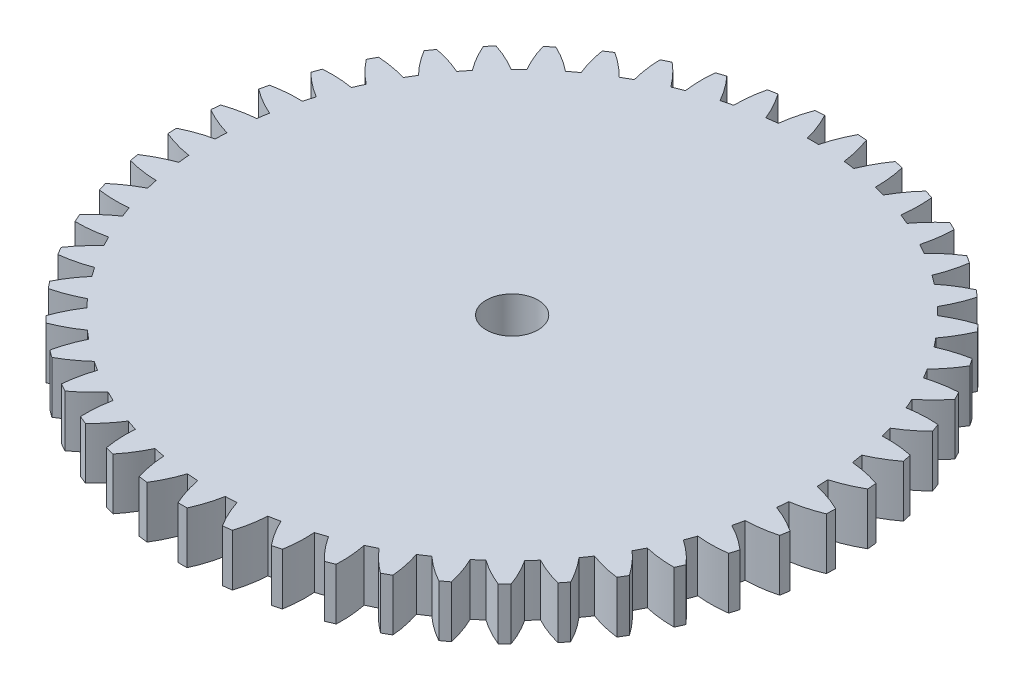
SolidWorks part; units mm, degrees
ref_plane "Front Plane" through (0, 0, 0) normal (0, 0, 1) x (1, 0, 0)
ref_plane "Top Plane" through (0, 0, 0) normal (0, 1, 0) x (1, 0, 0)
ref_plane "Right Plane" through (0, 0, 0) normal (1, 0, 0) x (0, 0, -1)
sketch "Sketch1" plane through (0, 0, 0) normal (0, 1, 0) x (1, 0, 0)
  circle A0 centre (0, 0) radius 1.5875
  circle A1 centre (0, 0) radius 18.3 construction
  arc A2 (-2.018, 18.3293) -> (-2.6973, 18.2417) centre (0, 0) ccw
  arc A3 (-20.1966, -0.3688) -> (-20.1788, -0.9259) centre (0, 0) ccw
  arc A4 (2.018, 18.3293) -> (1.5722, 20.1387) centre (-5.7243, 17.3817) ccw
  arc A5 (-0.3425, 18.4368) -> (-1.016, 20.1744) centre (-7.9, 16.507) ccw
  arc A6 (1.016, 20.1744) -> (0.3425, 18.4368) centre (7.9, 16.507) ccw
  arc A7 (3.5875, 19.8789) -> (2.6973, 18.2417) centre (9.946, 15.3612) ccw
  arc A8 (4.3453, 17.9207) -> (4.1346, 19.7723) centre (-3.4546, 17.971) ccw
  arc A9 (6.1001, 19.2569) -> (5.0079, 17.747) centre (11.8287, 13.9632) ccw
  arc A10 (6.6013, 17.2179) -> (6.6291, 19.0813) centre (-1.1281, 18.2652) ccw
  arc A11 (8.5125, 18.3188) -> (7.2362, 16.9609) centre (13.5172, 12.336) ccw
  arc A12 (8.7488, 16.2324) -> (9.0147, 18.0769) centre (1.2168, 18.2595) ccw
  arc A13 (10.7852, 17.0798) -> (9.3457, 15.8963) centre (14.9837, 10.5062) ccw
  arc A14 (10.7528, 14.9804) -> (11.2523, 16.7757) centre (3.5418, 17.954) ccw
  arc A15 (12.8808, 15.5604) -> (11.3017, 14.5707) centre (16.2042, 8.5038) ccw
  arc A16 (12.5801, 13.4823) -> (13.3052, 15.1991) centre (5.8087, 17.3537) ccw
  arc A17 (14.7648, 13.7855) -> (13.0722, 13.0058) centre (17.1586, 6.3619) ccw
  arc A18 (14.2009, 11.7629) -> (15.1396, 13.3729) centre (7.9801, 16.4684) ccw
  arc A19 (16.4065, 11.7842) -> (14.628, 11.2274) centre (17.8312, 4.1155) ccw
  arc A20 (15.5886, 9.8504) -> (16.7253, 11.3271) centre (10.0205, 15.3127) ccw
  arc A21 (17.7787, 9.5895) -> (15.9437, 9.2646) centre (18.2111, 1.8015) ccw
  arc A22 (16.7202, 7.7761) -> (18.0365, 9.0953) centre (11.8964, 13.9056) ccw
  arc A23 (18.859, 7.2373) -> (16.9975, 7.1497) centre (18.292, -0.5421) ccw
  arc A24 (17.5773, 5.5741) -> (19.0515, 6.7142) centre (13.5769, 12.2702) ccw
  arc A25 (19.6297, 4.7662) -> (17.7722, 4.9174) centre (18.0725, -2.8768) ccw
  arc A26 (18.1458, 3.2806) -> (19.7537, 4.2228) centre (15.0345, 10.4332) ccw
  arc A27 (20.078, 2.2169) -> (18.2552, 2.6044) centre (17.5562, -5.1642) ccw
  arc A28 (18.4164, 0.9333) -> (20.1315, 1.6621) centre (16.2453, 8.425) ccw
  arc A29 (20.1966, -0.3688) -> (18.4383, 0.2486) centre (16.7517, -7.3669) ccw
  arc A30 (18.3845, -1.4294) -> (20.1788, -0.9259) centre (17.1893, 6.2784) ccw
  arc A31 (19.9837, -2.9485) -> (18.3187, -2.1113) centre (15.6721, -9.4485) ccw
  arc A32 (18.0508, -3.7687) -> (19.8947, -3.4987) centre (17.851, 4.0288) ccw
  arc A33 (19.4425, -5.4797) -> (17.8984, -4.4365) centre (14.3352, -11.3751) ccw
  arc A34 (17.4207, -6.046) -> (19.284, -6.0141) centre (18.2197, 1.713) ccw
  arc A35 (18.5822, -7.921) -> (17.1841, -6.6889) centre (12.7629, -13.1148) ccw
  arc A36 (16.5045, -8.2241) -> (18.3566, -8.4307) centre (18.2891, -0.631) ccw
  arc A37 (17.4167, -10.2322) -> (16.1877, -8.8314) centre (10.981, -14.6392) ccw
  arc A38 (15.3173, -10.2671) -> (17.1278, -10.7089) centre (18.0583, -2.9646) ccw
  arc A39 (15.9653, -12.3754) -> (14.9254, -10.8289) centre (9.0188, -15.9233) ccw
  arc A40 (13.8786, -12.1415) -> (15.6177, -12.8112) centre (17.5309, -5.2495) ccw
  arc A41 (14.2517, -14.3154) -> (13.4181, -12.6486) centre (6.9086, -16.9458) ccw
  arc A42 (12.2121, -13.8166) -> (13.8512, -14.7032) centre (16.7157, -7.4482) ccw
  arc A43 (12.304, -16.0203) -> (11.6905, -14.2607) centre (4.6849, -17.6902) ccw
  arc A44 (10.345, -15.2648) -> (11.8573, -16.3537) centre (15.626, -9.5246) ccw
  arc A45 (10.1544, -17.4622) -> (9.7709, -15.6385) centre (2.3842, -18.144) ccw
  arc A46 (8.308, -16.4624) -> (9.6687, -17.7357) centre (14.2798, -11.4446) ccw
  arc A47 (7.838, -18.6174) -> (7.6909, -16.7596) centre (0.0445, -18.2999) ccw
  arc A48 (6.1346, -17.3896) -> (7.3213, -18.8265) centre (12.699, -13.1767) ccw
  arc A49 (5.3929, -19.4668) -> (5.4845, -17.6055) centre (-2.2961, -18.1554) ccw
  arc A50 (3.8605, -18.0314) -> (4.8538, -19.6082) centre (10.9098, -14.6924) ccw
  arc A51 (2.8593, -19.9966) -> (3.1882, -18.1623) centre (-4.5989, -17.7127) ccw
  arc A52 (1.523, -18.377) -> (2.3065, -20.0679) centre (8.9414, -15.9669) ccw
  arc A53 (0.2787, -20.1981) -> (0.8395, -18.4209) centre (-6.8262, -16.9792) ccw
  arc A54 (-0.8395, -18.4209) -> (-0.2787, -20.1981) centre (6.8262, -16.9792) ccw
  arc A55 (-2.3065, -20.0679) -> (-1.523, -18.377) centre (-8.9414, -15.9669) ccw
  arc A56 (-3.1882, -18.1623) -> (-2.8593, -19.9966) centre (4.5989, -17.7127) ccw
  arc A57 (-4.8538, -19.6082) -> (-3.8605, -18.0314) centre (-10.9098, -14.6924) ccw
  arc A58 (-5.4845, -17.6055) -> (-5.3929, -19.4668) centre (2.2961, -18.1554) ccw
  arc A59 (-7.3213, -18.8265) -> (-6.1346, -17.3896) centre (-12.699, -13.1767) ccw
  arc A60 (-7.6909, -16.7596) -> (-7.838, -18.6174) centre (-0.0445, -18.2999) ccw
  arc A61 (-9.6687, -17.7357) -> (-8.308, -16.4624) centre (-14.2798, -11.4446) ccw
  arc A62 (-9.7709, -15.6385) -> (-10.1544, -17.4622) centre (-2.3842, -18.144) ccw
  arc A63 (-11.8573, -16.3537) -> (-10.345, -15.2648) centre (-15.626, -9.5246) ccw
  arc A64 (-11.6905, -14.2607) -> (-12.304, -16.0203) centre (-4.6849, -17.6902) ccw
  arc A65 (-13.8512, -14.7032) -> (-12.2121, -13.8166) centre (-16.7157, -7.4482) ccw
  arc A66 (-13.4181, -12.6486) -> (-14.2517, -14.3154) centre (-6.9086, -16.9458) ccw
  arc A67 (-15.6177, -12.8112) -> (-13.8786, -12.1415) centre (-17.5309, -5.2495) ccw
  arc A68 (-14.9254, -10.8289) -> (-15.9653, -12.3754) centre (-9.0188, -15.9233) ccw
  arc A69 (-17.1278, -10.7089) -> (-15.3173, -10.2671) centre (-18.0583, -2.9646) ccw
  arc A70 (-16.1877, -8.8314) -> (-17.4167, -10.2322) centre (-10.981, -14.6392) ccw
  arc A71 (-18.3566, -8.4307) -> (-16.5045, -8.2241) centre (-18.2891, -0.631) ccw
  arc A72 (-17.1841, -6.6889) -> (-18.5822, -7.921) centre (-12.7629, -13.1148) ccw
  arc A73 (-19.284, -6.0141) -> (-17.4207, -6.046) centre (-18.2197, 1.713) ccw
  arc A74 (-17.8984, -4.4365) -> (-19.4425, -5.4797) centre (-14.3352, -11.3751) ccw
  arc A75 (-19.8947, -3.4987) -> (-18.0508, -3.7687) centre (-17.851, 4.0288) ccw
  arc A76 (-18.3187, -2.1113) -> (-19.9837, -2.9485) centre (-15.6721, -9.4485) ccw
  arc A77 (-20.1788, -0.9259) -> (-18.3845, -1.4294) centre (-17.1893, 6.2784) ccw
  arc A78 (-18.4383, 0.2486) -> (-20.1966, -0.3688) centre (-16.7517, -7.3669) ccw
  arc A79 (-20.1315, 1.6621) -> (-18.4164, 0.9333) centre (-16.2453, 8.425) ccw
  arc A80 (-18.2552, 2.6044) -> (-20.078, 2.2169) centre (-17.5562, -5.1642) ccw
  arc A81 (-19.7537, 4.2228) -> (-18.1458, 3.2806) centre (-15.0345, 10.4332) ccw
  arc A82 (-17.7722, 4.9174) -> (-19.6297, 4.7662) centre (-18.0725, -2.8768) ccw
  arc A83 (-19.0515, 6.7142) -> (-17.5773, 5.5741) centre (-13.5769, 12.2702) ccw
  arc A84 (-16.9975, 7.1497) -> (-18.859, 7.2373) centre (-18.292, -0.5421) ccw
  arc A85 (-18.0365, 9.0953) -> (-16.7202, 7.7761) centre (-11.8964, 13.9056) ccw
  arc A86 (-15.9437, 9.2646) -> (-17.7787, 9.5895) centre (-18.2111, 1.8015) ccw
  arc A87 (-16.7253, 11.3271) -> (-15.5886, 9.8504) centre (-10.0205, 15.3127) ccw
  arc A88 (-14.628, 11.2274) -> (-16.4065, 11.7842) centre (-17.8312, 4.1155) ccw
  arc A89 (-15.1396, 13.3729) -> (-14.2009, 11.7629) centre (-7.9801, 16.4684) ccw
  arc A90 (-13.0722, 13.0058) -> (-14.7648, 13.7855) centre (-17.1586, 6.3619) ccw
  arc A91 (-13.3052, 15.1991) -> (-12.5801, 13.4823) centre (-5.8087, 17.3537) ccw
  arc A92 (-11.3017, 14.5707) -> (-12.8808, 15.5604) centre (-16.2042, 8.5038) ccw
  arc A93 (-11.2523, 16.7757) -> (-10.7528, 14.9804) centre (-3.5418, 17.954) ccw
  arc A94 (-9.3457, 15.8963) -> (-10.7852, 17.0798) centre (-14.9837, 10.5062) ccw
  arc A95 (-9.0147, 18.0769) -> (-8.7488, 16.2324) centre (-1.2168, 18.2595) ccw
  arc A96 (-7.2362, 16.9609) -> (-8.5125, 18.3188) centre (-13.5172, 12.336) ccw
  arc A97 (-6.6291, 19.0813) -> (-6.6013, 17.2179) centre (1.1281, 18.2652) ccw
  arc A98 (-5.0079, 17.747) -> (-6.1001, 19.2569) centre (-11.8287, 13.9632) ccw
  arc A99 (-4.1346, 19.7723) -> (-4.3453, 17.9207) centre (3.4546, 17.971) ccw
  arc A100 (-2.6973, 18.2417) -> (-3.5875, 19.8789) centre (-9.946, 15.3612) ccw
  arc A101 (-1.5722, 20.1387) -> (-2.018, 18.3293) centre (5.7243, 17.3817) ccw
  arc A102 (0.3425, 18.4368) -> (-0.3425, 18.4368) centre (0, 0) ccw
  arc A103 (-4.3453, 17.9207) -> (-5.0079, 17.747) centre (0, 0) ccw
  arc A104 (-6.6013, 17.2179) -> (-7.2362, 16.9609) centre (0, 0) ccw
  arc A105 (2.6973, 18.2417) -> (2.018, 18.3293) centre (0, 0) ccw
  arc A106 (5.0079, 17.747) -> (4.3453, 17.9207) centre (0, 0) ccw
  arc A107 (7.2362, 16.9609) -> (6.6013, 17.2179) centre (0, 0) ccw
  arc A108 (-8.7488, 16.2324) -> (-9.3457, 15.8963) centre (0, 0) ccw
  arc A109 (-10.7528, 14.9804) -> (-11.3017, 14.5707) centre (0, 0) ccw
  arc A110 (-12.5801, 13.4823) -> (-13.0722, 13.0058) centre (0, 0) ccw
  arc A111 (-14.2009, 11.7629) -> (-14.628, 11.2274) centre (0, 0) ccw
  arc A112 (-15.5886, 9.8504) -> (-15.9437, 9.2646) centre (0, 0) ccw
  arc A113 (-16.7202, 7.7761) -> (-16.9975, 7.1497) centre (0, 0) ccw
  arc A114 (-17.5773, 5.5741) -> (-17.7722, 4.9174) centre (0, 0) ccw
  arc A115 (-18.1458, 3.2806) -> (-18.2552, 2.6044) centre (0, 0) ccw
  arc A116 (-18.4164, 0.9333) -> (-18.4383, 0.2486) centre (0, 0) ccw
  arc A117 (-18.3845, -1.4294) -> (-18.3187, -2.1113) centre (0, 0) ccw
  arc A118 (-20.078, 2.2169) -> (-20.1315, 1.6621) centre (0, 0) ccw
  arc A119 (-19.6297, 4.7662) -> (-19.7537, 4.2228) centre (0, 0) ccw
  arc A120 (-18.859, 7.2373) -> (-19.0515, 6.7142) centre (0, 0) ccw
  arc A121 (-17.7787, 9.5895) -> (-18.0365, 9.0953) centre (0, 0) ccw
  arc A122 (-16.4065, 11.7842) -> (-16.7253, 11.3271) centre (0, 0) ccw
  arc A123 (-14.7648, 13.7855) -> (-15.1396, 13.3729) centre (0, 0) ccw
  arc A124 (-12.8808, 15.5604) -> (-13.3052, 15.1991) centre (0, 0) ccw
  arc A125 (-10.7852, 17.0798) -> (-11.2523, 16.7757) centre (0, 0) ccw
  arc A126 (6.6291, 19.0813) -> (6.1001, 19.2569) centre (0, 0) ccw
  arc A127 (4.1346, 19.7723) -> (3.5875, 19.8789) centre (0, 0) ccw
  arc A128 (1.5722, 20.1387) -> (1.016, 20.1744) centre (0, 0) ccw
  arc A129 (-1.016, 20.1744) -> (-1.5722, 20.1387) centre (0, 0) ccw
  arc A130 (-3.5875, 19.8789) -> (-4.1346, 19.7723) centre (0, 0) ccw
  arc A131 (-6.1001, 19.2569) -> (-6.6291, 19.0813) centre (0, 0) ccw
  arc A132 (-8.5125, 18.3188) -> (-9.0147, 18.0769) centre (0, 0) ccw
  arc A133 (9.0147, 18.0769) -> (8.5125, 18.3188) centre (0, 0) ccw
  arc A134 (11.2523, 16.7757) -> (10.7852, 17.0798) centre (0, 0) ccw
  arc A135 (13.3052, 15.1991) -> (12.8808, 15.5604) centre (0, 0) ccw
  arc A136 (15.1396, 13.3729) -> (14.7648, 13.7855) centre (0, 0) ccw
  arc A137 (16.7253, 11.3271) -> (16.4065, 11.7842) centre (0, 0) ccw
  arc A138 (18.0365, 9.0953) -> (17.7787, 9.5895) centre (0, 0) ccw
  arc A139 (19.0515, 6.7142) -> (18.859, 7.2373) centre (0, 0) ccw
  arc A140 (15.9437, 9.2646) -> (15.5886, 9.8504) centre (0, 0) ccw
  arc A141 (14.628, 11.2274) -> (14.2009, 11.7629) centre (0, 0) ccw
  arc A142 (13.0722, 13.0058) -> (12.5801, 13.4823) centre (0, 0) ccw
  arc A143 (11.3017, 14.5707) -> (10.7528, 14.9804) centre (0, 0) ccw
  arc A144 (9.3457, 15.8963) -> (8.7488, 16.2324) centre (0, 0) ccw
  arc A145 (-19.9837, -2.9485) -> (-19.8947, -3.4987) centre (0, 0) ccw
  arc A146 (-19.4425, -5.4797) -> (-19.284, -6.0141) centre (0, 0) ccw
  arc A147 (-18.5822, -7.921) -> (-18.3566, -8.4307) centre (0, 0) ccw
  arc A148 (-17.4167, -10.2322) -> (-17.1278, -10.7089) centre (0, 0) ccw
  arc A149 (-15.9653, -12.3754) -> (-15.6177, -12.8112) centre (0, 0) ccw
  arc A150 (-14.2517, -14.3154) -> (-13.8512, -14.7032) centre (0, 0) ccw
  arc A151 (-12.304, -16.0203) -> (-11.8573, -16.3537) centre (0, 0) ccw
  arc A152 (-10.1544, -17.4622) -> (-9.6687, -17.7357) centre (0, 0) ccw
  arc A153 (-7.838, -18.6174) -> (-7.3213, -18.8265) centre (0, 0) ccw
  arc A154 (-5.3929, -19.4668) -> (-4.8538, -19.6082) centre (0, 0) ccw
  arc A155 (7.3213, -18.8265) -> (7.838, -18.6174) centre (0, 0) ccw
  arc A156 (9.6687, -17.7357) -> (10.1544, -17.4622) centre (0, 0) ccw
  arc A157 (11.8573, -16.3537) -> (12.304, -16.0203) centre (0, 0) ccw
  arc A158 (13.8512, -14.7032) -> (14.2517, -14.3154) centre (0, 0) ccw
  arc A159 (15.6177, -12.8112) -> (15.9653, -12.3754) centre (0, 0) ccw
  arc A160 (17.1278, -10.7089) -> (17.4167, -10.2322) centre (0, 0) ccw
  arc A161 (14.9254, -10.8289) -> (15.3173, -10.2671) centre (0, 0) ccw
  arc A162 (13.4181, -12.6486) -> (13.8786, -12.1415) centre (0, 0) ccw
  arc A163 (11.6905, -14.2607) -> (12.2121, -13.8166) centre (0, 0) ccw
  arc A164 (9.7709, -15.6385) -> (10.345, -15.2648) centre (0, 0) ccw
  arc A165 (7.6909, -16.7596) -> (8.308, -16.4624) centre (0, 0) ccw
  arc A166 (5.4845, -17.6055) -> (6.1346, -17.3896) centre (0, 0) ccw
  arc A167 (3.1882, -18.1623) -> (3.8605, -18.0314) centre (0, 0) ccw
  arc A168 (0.8395, -18.4209) -> (1.523, -18.377) centre (0, 0) ccw
  arc A169 (-1.523, -18.377) -> (-0.8395, -18.4209) centre (0, 0) ccw
  arc A170 (-3.8605, -18.0314) -> (-3.1882, -18.1623) centre (0, 0) ccw
  arc A171 (-6.1346, -17.3896) -> (-5.4845, -17.6055) centre (0, 0) ccw
  arc A172 (-8.308, -16.4624) -> (-7.6909, -16.7596) centre (0, 0) ccw
  arc A173 (-10.345, -15.2648) -> (-9.7709, -15.6385) centre (0, 0) ccw
  arc A174 (-12.2121, -13.8166) -> (-11.6905, -14.2607) centre (0, 0) ccw
  arc A175 (-13.8786, -12.1415) -> (-13.4181, -12.6486) centre (0, 0) ccw
  arc A176 (-15.3173, -10.2671) -> (-14.9254, -10.8289) centre (0, 0) ccw
  arc A177 (-16.5045, -8.2241) -> (-16.1877, -8.8314) centre (0, 0) ccw
  arc A178 (-17.4207, -6.046) -> (-17.1841, -6.6889) centre (0, 0) ccw
  arc A179 (-18.0508, -3.7687) -> (-17.8984, -4.4365) centre (0, 0) ccw
  arc A180 (2.3065, -20.0679) -> (2.8593, -19.9966) centre (0, 0) ccw
  arc A181 (4.8538, -19.6082) -> (5.3929, -19.4668) centre (0, 0) ccw
  arc A182 (-0.2787, -20.1981) -> (0.2787, -20.1981) centre (0, 0) ccw
  arc A183 (-2.8593, -19.9966) -> (-2.3065, -20.0679) centre (0, 0) ccw
  arc A184 (18.3566, -8.4307) -> (18.5822, -7.921) centre (0, 0) ccw
  arc A185 (19.284, -6.0141) -> (19.4425, -5.4797) centre (0, 0) ccw
  arc A186 (19.8947, -3.4987) -> (19.9837, -2.9485) centre (0, 0) ccw
  arc A187 (20.1788, -0.9259) -> (20.1966, -0.3688) centre (0, 0) ccw
  arc A188 (20.1315, 1.6621) -> (20.078, 2.2169) centre (0, 0) ccw
  arc A189 (19.7537, 4.2228) -> (19.6297, 4.7662) centre (0, 0) ccw
  arc A190 (17.7722, 4.9174) -> (17.5773, 5.5741) centre (0, 0) ccw
  arc A191 (16.9975, 7.1497) -> (16.7202, 7.7761) centre (0, 0) ccw
  arc A192 (18.2552, 2.6044) -> (18.1458, 3.2806) centre (0, 0) ccw
  arc A193 (18.4383, 0.2486) -> (18.4164, 0.9333) centre (0, 0) ccw
  arc A194 (18.3187, -2.1113) -> (18.3845, -1.4294) centre (0, 0) ccw
  arc A195 (17.8984, -4.4365) -> (18.0508, -3.7687) centre (0, 0) ccw
  arc A196 (17.1841, -6.6889) -> (17.4207, -6.046) centre (0, 0) ccw
  arc A197 (16.1877, -8.8314) -> (16.5045, -8.2241) centre (0, 0) ccw
  point P7 (0.3425, 18.4368)
  point P10 (-0.3425, 18.4368)
  point P304 (0, 0)
  dimension "D1" = 20.2
  dimension "D2" = 18.44
  dimension "D3" = 18.3
  dimension "D4" = 3.175
  dimension "D5" = 0.685
  dimension "D6" = 7.8
  dimension "D8" = 7.8
  dimension "D7" = 0.3425
  dimension "D9" = 49
extrude "Boss-Extrude1" add sketch "Sketch1" along normal blind 3.175
